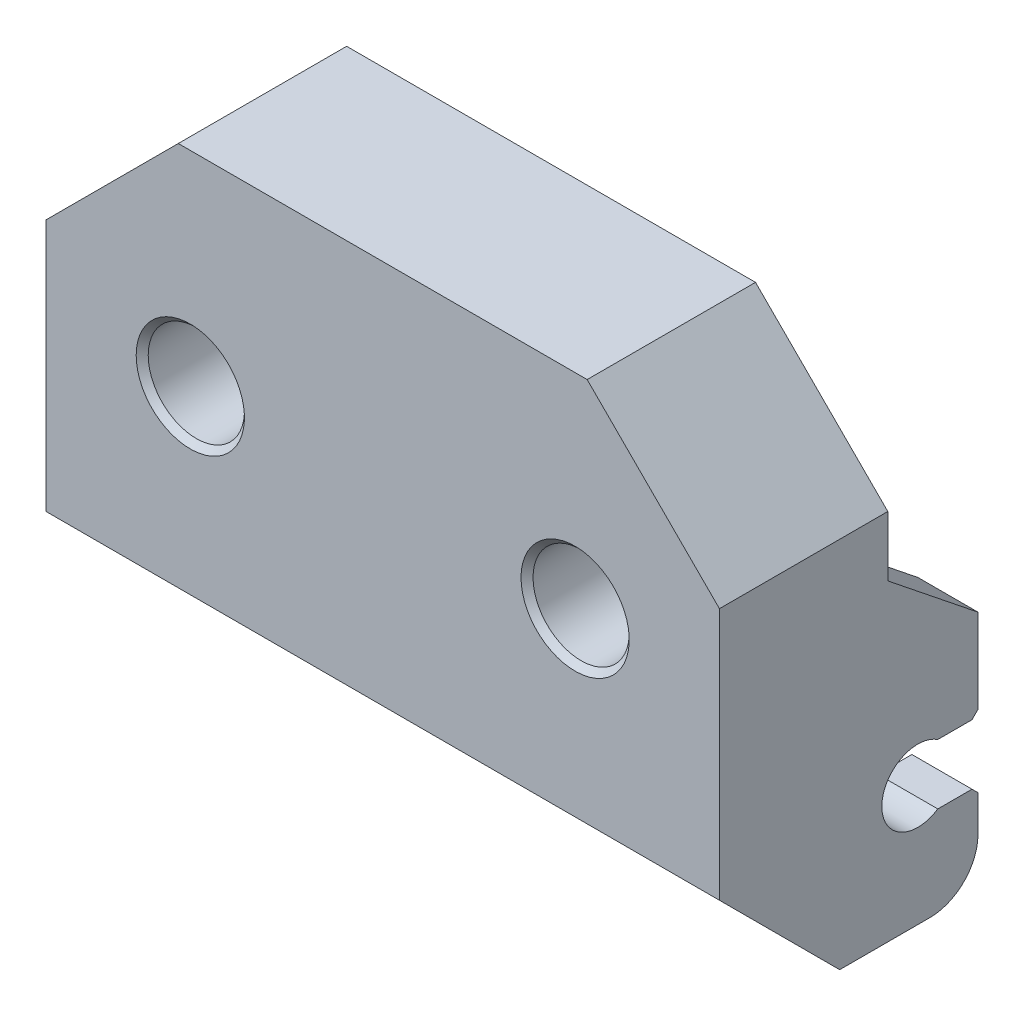
SolidWorks part; units mm, degrees
material "ABS"
ref_plane "Plan de face" through (0, 0, 0) normal (0, 0, 1) x (1, 0, 0)
ref_plane "Plan de dessus" through (0, 0, 0) normal (0, 1, 0) x (1, 0, 0)
ref_plane "Plan de droite" through (0, 0, 0) normal (1, 0, 0) x (0, 0, -1)
sketch "Esquisse3" plane through (0, 0, 0) normal (0, 0, 1) x (1, 0, 0)
  line L0 (-5.3714, 0) -> (17.6286, 0)
  line L1 (17.6286, 0) -> (17.6286, -18.5)
  line L2 (17.6286, -18.5) -> (20.1286, -18.5)
  line L3 (20.1286, -18.5) -> (20.1286, 2.5)
  line L4 (20.1286, 2.5) -> (-7.8714, 2.5)
  line L5 (-7.8714, 2.5) -> (-7.8714, -18.5)
  line L6 (-7.8714, -18.5) -> (-5.3714, -18.5)
  line L7 (-5.3714, -18.5) -> (-5.3714, 0)
  dimension "D1" = 2.5
  dimension "D2" = 2.5
  dimension "D3" = 28
  dimension "D4" = 21
  dimension "D5" = 21
  dimension "D6" = 2.5
extrude "Boss.-Extru.1" add sketch "Esquisse3" along normal blind 7
chamfer "Chanfrein2" distance 4 angle 45 2 edges at (-5.3714, 0, 3.5) (17.6286, 0, 3.5)
chamfer "Chanfrein3" distance 5.5 angle 45 2 edges at (20.1286, 2.5, 3.5) (-7.8714, 2.5, 3.5)
chamfer "Chanfrein4" distance 5 angle 45 2 edges at (18.8786, -18.5, 7) (-6.6214, -18.5, 7)
sketch "Esquisse4" plane through (0, 0, 7) normal (0, 0, 1) x (1, 0, 0)
  line L0 (-5.3714, -13.5) -> (17.6286, -13.5)
  line L1 (17.6286, -13.5) -> (17.6286, -4)
  line L2 (17.6286, -4) -> (13.6286, 0)
  line L3 (13.6286, 0) -> (-1.3714, 0)
  line L4 (-1.3714, 0) -> (-5.3714, -4)
  line L5 (-5.3714, -4) -> (-5.3714, -13.5)
extrude "Boss.-Extru.2" add sketch "Esquisse4" against normal blind 1.5
sketch "Esquisse5" plane through (0, 0, 5.5) normal (0, 0, -1) x (-1, 0, 0)
  line L1 (-17.6286, -13.5) -> (-8.6286, -13.5)
  line L2 (-17.6286, -13.5) -> (-17.6286, -12.25)
  line L3 (-17.6286, -12.25) -> (-8.6286, -12.25)
  line L4 (-8.6286, -13.5) -> (-8.6286, -12.25)
  line L5 (5.3714, -13.5) -> (-3.6286, -13.5)
  line L6 (5.3714, -13.5) -> (5.3714, -12.25)
  line L7 (5.3714, -12.25) -> (-3.6286, -12.25)
  line L8 (-3.6286, -13.5) -> (-3.6286, -12.25)
  dimension "D1" = 1.25
  dimension "D2" = 1.25
  dimension "D3" = 9
  dimension "D4" = 9
extrude "Boss.-Extru.3" add sketch "Esquisse5" along normal blind 4
sketch "Esquisse6" plane through (0, -13.5, 0) normal (0, -1, 0) x (1, 0, 0)
  line L0 (17.6286, 1.5) -> (8.6286, 5.5)
  line L1 (8.6286, 5.5) -> (8.6286, 1.5)
  line L2 (8.6286, 1.5) -> (17.6286, 1.5)
  line L3 (-5.3714, 1.5) -> (3.6286, 5.5)
  line L4 (3.6286, 5.5) -> (3.6286, 1.5)
  line L5 (3.6286, 1.5) -> (-5.3714, 1.5)
extrude "Enlèv. mat.-Extru.1" cut sketch "Esquisse6" against normal up to surface (1.25 mm away) up to face at (-0.8714, -12.25, 3.5)
sketch "Esquisse7" plane through (0, 0, 5.5) normal (0, 0, -1) x (-1, 0, 0)
  line L0 (-14.1286, -6) -> (1.8714, -6) construction
  line L1 (-6.1286, 0) -> (-6.1286, -6) construction
  line L2 (-13.6286, 0) -> (1.3714, 0) construction
  circle A0 centre (-14.1286, -6) radius 2.75
  circle A1 centre (1.8714, -6) radius 2.75
  dimension "D1" = 5.5
  dimension "D2" = 5.5
  dimension "D3" = 16
  dimension "D4" = 0
  dimension "D5" = 6
extrude "Boss.-Extru.4" add sketch "Esquisse7" along normal up to surface (5.5 mm away) up to face at (6.1286, -6.9167, 0)
sketch "Esquisse9" plane through (0, 0, 0) normal (0, 0, -1) x (-1, 0, 0)
  circle A0 centre (-14.1286, -6) radius 2
  circle A1 centre (1.8714, -6) radius 2
  dimension "D1" = 4
  dimension "D2" = 4
extrude "Enlèv. mat.-Extru.2" cut sketch "Esquisse9" against normal up to surface (4.5 mm away) from offset 2.5 up to face at (6.1286, -6.875, 7) offset against normal yes
sketch "Esquisse10" plane through (0, 0, 0) normal (0, 0, -1) x (-1, 0, 0)
  line L0 (-16.8786, -6) -> (-17.6286, -6) construction
  line L1 (-17.6286, -4) -> (-17.6286, -18.5) construction
  line L2 (-14.1286, -3.25) -> (-14.1286, -0.5) construction
  line L3 (-17.6286, -4) -> (-13.6286, 0) construction
  line L4 (1.8714, -3.25) -> (1.8714, -0.5) construction
  line L5 (-17.78, -6.5) -> (-16.7271, -6.5)
  line L6 (-17.78, -6.5) -> (-17.78, -5.5)
  line L7 (-17.78, -5.5) -> (-16.7271, -5.5)
  line L8 (-16.7271, -6.5) -> (-16.7271, -5.5)
  line L9 (-17.78, -6.5) -> (-16.7271, -5.5) construction
  line L10 (-17.78, -5.5) -> (-16.7271, -6.5) construction
  line L11 (-14.6286, -3.75) -> (-13.6286, -3.75)
  line L12 (-14.6286, -3.75) -> (-14.6286, 0)
  line L13 (-14.6286, 0) -> (-13.6286, 0)
  line L14 (-13.6286, -3.75) -> (-13.6286, 0)
  line L15 (-14.6286, -3.75) -> (-13.6286, 0) construction
  line L16 (-14.6286, 0) -> (-13.6286, -3.75) construction
  line L17 (1.3714, 0) -> (5.3714, -4) construction
  line L18 (4.6214, -6) -> (5.3714, -6) construction
  line L19 (5.3714, -18.5) -> (5.3714, -4) construction
  line L21 (1.3714, -3.8502) -> (2.3714, -3.8502)
  line L22 (1.3714, -3.8502) -> (1.3714, 0.1002)
  line L23 (1.3714, 0.1002) -> (2.3714, 0.1002)
  line L24 (2.3714, -3.8502) -> (2.3714, 0.1002)
  line L25 (1.3714, -3.8502) -> (2.3714, 0.1002) construction
  line L26 (1.3714, 0.1002) -> (2.3714, -3.8502) construction
  line L27 (4.3999, -6.5) -> (5.593, -6.5)
  line L28 (4.3999, -6.5) -> (4.3999, -5.5)
  line L29 (4.3999, -5.5) -> (5.593, -5.5)
  line L30 (5.593, -6.5) -> (5.593, -5.5)
  line L31 (4.3999, -6.5) -> (5.593, -5.5) construction
  line L32 (4.3999, -5.5) -> (5.593, -6.5) construction
  circle A0 centre (-14.1286, -6) radius 2.75 construction
  circle A1 centre (1.8714, -6) radius 2.75 construction
  point P11 (-17.2536, -6)
  point P16 (-14.1286, -1.875)
  point P32 (1.8714, -1.875)
  point P37 (4.9964, -6)
  dimension "D1" = 1
  dimension "D2" = 1
  dimension "D3" = 1
  dimension "D4" = 1
extrude "Boss.-Extru.5" add sketch "Esquisse10" against normal up to surface (5.5 mm away) up to face at (0.8786, -6, 5.5)
sketch "Esquisse11" plane through (0, 0, 0) normal (0, 0, -1) x (-1, 0, 0)
  line L0 (5.3714, -18.5) -> (5.3714, -6.5) construction
  line L1 (7.8714, -18.5) -> (5.3714, -18.5)
  line L2 (7.8714, -18.5) -> (7.8714, -8.5)
  line L3 (7.8714, -8.5) -> (5.3714, -8.5)
  line L4 (5.3714, -18.5) -> (5.3714, -8.5)
  line L5 (-17.6286, -6.5) -> (-17.6286, -18.5) construction
  line L6 (-20.1286, -18.5) -> (-17.6286, -18.5)
  line L7 (-20.1286, -18.5) -> (-20.1286, -8.5)
  line L8 (-20.1286, -8.5) -> (-17.6286, -8.5)
  line L9 (-17.6286, -18.5) -> (-17.6286, -8.5)
  dimension "D1" = 10
  dimension "D2" = 10
extrude "Boss.-Extru.6" add sketch "Esquisse11" along normal blind 3.75
sketch "Esquisse12" plane through (-5.3714, 0, 0) normal (1, 0, 0) x (0, 0, -1)
  line L0 (3.75, -8.5) -> (3.75, -18.5) construction
  line L1 (1.25, -13.5) -> (3.75, -13.5) construction
  line L2 (3.75, -14.75) -> (3.75, -12.25)
  line L4 (3.75, -14.75) -> (2.0792, -14.75)
  line L5 (3.75, -12.25) -> (2.0792, -12.25)
  arc A1 (2.0792, -12.25) -> (2.0792, -14.75) centre (1.25, -13.5) ccw
  circle A2 centre (1.25, -13.5) radius 1.5 construction
  point P7 (3.75, -13.5)
  dimension "D2" = 3
  dimension "D1" = 2.5
  dimension "D4" = 2.5
  dimension "D5" = 1.25
extrude "Enlèv. mat.-Extru.3" cut sketch "Esquisse12" against normal up to surface and the other way up to surface from offset 11.5
sketch "Esquisse13" plane through (0, -8.5, 0) normal (0, 1, 0) x (1, 0, 0)
  line L0 (17.6286, 0) -> (20.1286, 0) construction
  line L1 (20.1286, 0) -> (20.1286, 3.75) construction
  line L2 (20.1286, 3.75) -> (17.6286, 3.75) construction
  line L3 (17.6286, 3.75) -> (17.6286, 0) construction
  line L4 (-7.8714, 0) -> (-5.3714, 0) construction
  line L5 (-5.3714, 0) -> (-5.3714, 3.75) construction
  line L6 (-5.3714, 3.75) -> (-7.8714, 3.75) construction
  line L7 (-7.8714, 3.75) -> (-7.8714, 0) construction
  line L8 (17.6286, 0) -> (20.1286, 0)
  line L9 (20.1286, 0) -> (20.1286, 3.75)
  line L10 (20.1286, 3.75) -> (17.6286, 3.75)
  line L11 (17.6286, 3.75) -> (17.6286, 0)
  line L12 (-7.8714, 0) -> (-5.3714, 0)
  line L13 (-5.3714, 0) -> (-5.3714, 3.75)
  line L14 (-5.3714, 3.75) -> (-7.8714, 3.75)
  line L15 (-7.8714, 3.75) -> (-7.8714, 0)
extrude "Boss.-Extru.7" add sketch "Esquisse13" along normal blind 3
sketch "Esquisse14" plane through (-7.8714, 0, 0) normal (-1, 0, 0) x (0, 0, 1)
  line L0 (-3.75, -5.5) -> (-3.75, -8.5)
  line L1 (-3.75, -12.25) -> (-3.75, -5.5) construction
  line L2 (-3.75, -8.5) -> (0, -5.5)
  line L3 (0, -5.5) -> (-3.75, -5.5)
  dimension "D1" = 3
extrude "Enlèv. mat.-Extru.4" cut sketch "Esquisse14" against normal up to surface (28 mm away) up to face at (20.1286, -11.0455, -0.0754)
fillet "Congé1" radius 2 2 edges at (18.8786, -18.5, -3.75) (-6.6214, -18.5, -3.75)
chamfer "Chanfrein7" distance 0.25 angle 45 4 edges at (18.8786, -14.75, -3.75) (18.8786, -12.25, -3.75) (-6.6214, -12.25, -3.75) (-6.6214, -14.75, -3.75)
chamfer "Chanfrein8" distance 0.25 angle 45 2 edges at (-3.8714, -6, 7) (12.1286, -6, 7)
